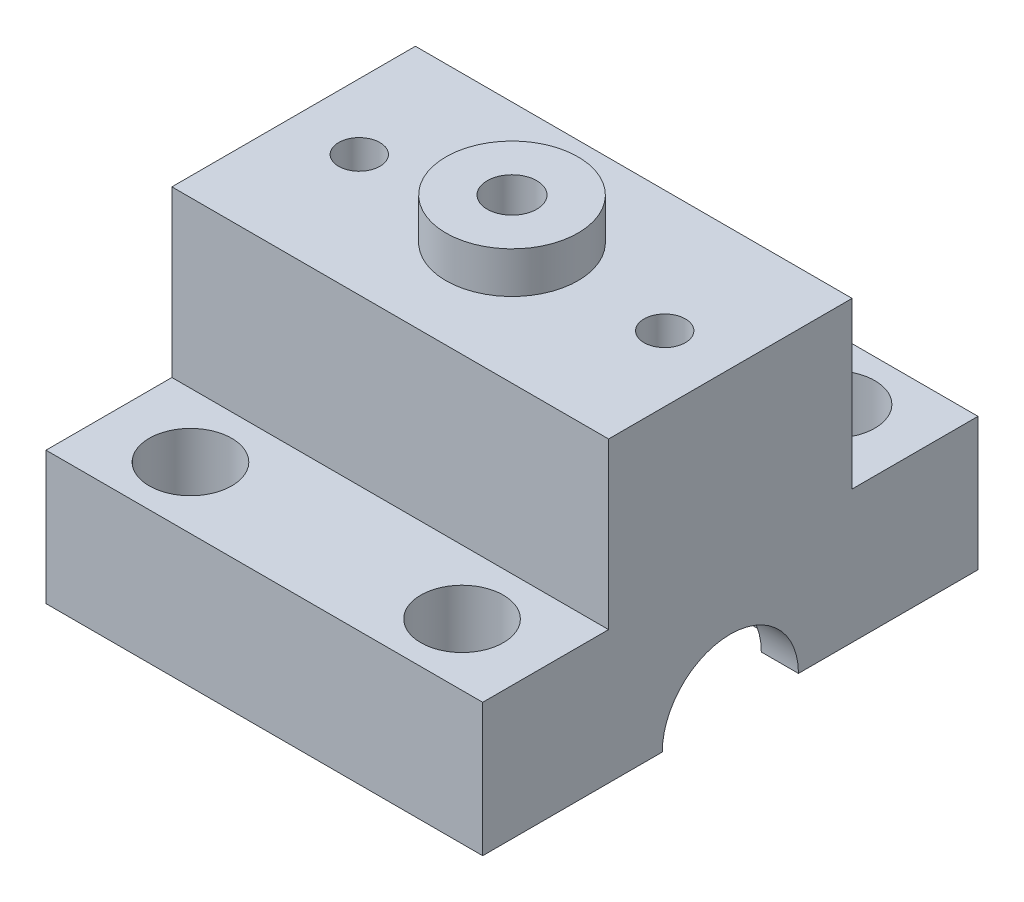
SolidWorks part; units mm, degrees
material "1060 Alloy"
ref_plane "Front Plane" through (0, 0, 0) normal (0, 0, 1) x (1, 0, 0)
ref_plane "Top Plane" through (0, 0, 0) normal (0, 1, 0) x (1, 0, 0)
ref_plane "Right Plane" through (0, 0, 0) normal (1, 0, 0) x (0, 0, -1)
sketch "Sketch1" plane through (0, 0, 0) normal (0, 1, 0) x (1, 0, 0)
  line L1 (-26.45, 15) -> (26.45, 15)
  line L2 (-26.45, 15) -> (-26.45, -15)
  line L3 (-26.45, -15) -> (26.45, -15)
  line L4 (26.45, 15) -> (26.45, -15)
  line L5 (-26.45, 15) -> (26.45, -15) construction
  line L6 (-26.45, -15) -> (26.45, 15) construction
  circle A0 centre (0, 0) radius 10.25
  point P0 (0, 0)
  dimension "D3" = 20.5
  dimension "D1" = 52.9
  dimension "D2" = 30
extrude "Boss-Extrude1" add sketch "Sketch1" along normal blind 5
sketch "Sketch2" plane through (0, 0, 0) normal (0, -1, 0) x (1, 0, 0)
  line L0 (-21.95, 10.5) -> (-21.95, -10.5)
  line L1 (-26.45, 15) -> (26.45, 15)
  line L2 (-26.45, 15) -> (-26.45, -15)
  line L3 (-26.45, -15) -> (26.45, -15)
  line L4 (26.45, 15) -> (26.45, -15)
  line L5 (-21.95, -10.5) -> (21.95, -10.5)
  line L6 (21.95, 10.5) -> (21.95, -10.5)
  line L7 (-21.95, 10.5) -> (21.95, 10.5)
  dimension "D1" = 4.5
extrude "Boss-Extrude2" add sketch "Sketch2" along normal blind 11.1
sketch "Sketch3" plane through (26.45, 0, 0) normal (1, 0, 0) x (0, 0, -1)
  line L0 (15, -11.1) -> (-15, -11.1) construction
  circle A0 centre (0, -11.1) radius 8.25
  dimension "D1" = 16.5
extrude "Cut-Extrude1" cut sketch "Sketch3" against normal through all
sketch "Sketch4" plane through (0, 0, -15) normal (0, 0, -1) x (-1, 0, 0)
  line L0 (26.45, 5) -> (26.45, -11.1) construction
  line L1 (-26.45, -11.1) -> (26.45, -11.1)
  line L2 (-26.45, -11.1) -> (-26.45, -6.1)
  line L3 (-26.45, -6.1) -> (26.45, -6.1)
  line L4 (26.45, -11.1) -> (26.45, -6.1)
  dimension "D1" = 5
extrude "Boss-Extrude3" add sketch "Sketch4" along normal blind 15
sketch "Sketch5" plane through (0, 0, 15) normal (0, 0, 1) x (1, 0, 0)
  line L0 (26.45, 5) -> (26.45, -11.1) construction
  line L1 (-26.45, -11.1) -> (26.45, -11.1)
  line L2 (-26.45, -11.1) -> (-26.45, -6.1)
  line L3 (-26.45, -6.1) -> (26.45, -6.1)
  line L4 (26.45, -11.1) -> (26.45, -6.1)
  dimension "D1" = 5
extrude "Boss-Extrude4" add sketch "Sketch5" along normal blind 15
sketch "Sketch7" plane through (0, 5, 0) normal (0, 1, 0) x (1, 0, 0)
  circle A0 centre (0, 0) radius 10.25
  circle A1 centre (0, 0) radius 14.75
  dimension "D1" = 4.5
extrude "Boss-Extrude5" add sketch "Sketch7" along normal blind 15
sketch "Sketch8" plane through (0, 20, 0) normal (0, 1, 0) x (1, 0, 0)
  circle A0 centre (0, 0) radius 14.75
  circle A1 centre (0, 0) radius 1.65
  dimension "D1" = 3.3
  dimension "D2" = 29.5
extrude "Boss-Extrude6" add sketch "Sketch8" along normal blind 5
sketch "Sketch9" plane through (0, 25, 0) normal (0, 1, 0) x (1, 0, 0)
  circle A0 centre (0, 0) radius 3
  circle A1 centre (0, 0) radius 8
  dimension "D1" = 6
  dimension "D2" = 5
extrude "Boss-Extrude7" add sketch "Sketch9" along normal blind 5
sketch "Sketch10" plane through (0, -6.1, 0) normal (0, 1, 0) x (1, 0, 0)
  line L1 (26.45, 30) -> (-26.45, 30)
  line L2 (26.45, 30) -> (26.45, 15)
  line L3 (26.45, 15) -> (-26.45, 15)
  line L4 (-26.45, 30) -> (-26.45, 15)
  line L5 (26.45, -15) -> (-26.45, -15)
  line L6 (26.45, -15) -> (26.45, -30)
  line L7 (26.45, -30) -> (-26.45, -30)
  line L8 (-26.45, -15) -> (-26.45, -30)
extrude "Boss-Extrude8" add sketch "Sketch10" along normal up to surface (11.1 mm away) up to face at (0, 5, 0)
sketch "Sketch11" plane through (0, -11.1, 0) normal (0, -1, 0) x (1, 0, 0)
  line L0 (-26.45, 30) -> (26.45, 30) construction
  line L1 (-26.45, 30) -> (-26.45, 8.25) construction
  line L2 (26.45, -30) -> (26.45, -8.25) construction
  line L3 (26.45, -30) -> (-26.45, -30) construction
  circle A0 centre (-16.45, 22.5) radius 2.5
  circle A1 centre (16.45, 22.5) radius 2.5
  circle A2 centre (16.45, -22.5) radius 2.5
  circle A3 centre (-16.45, -22.5) radius 2.5
  dimension "D1" = 7.5
  dimension "D2" = 10
  dimension "D3" = 10
  dimension "D4" = 7.5
  dimension "D5" = 5
  dimension "D6" = 5
  dimension "D7" = 5
  dimension "D8" = 5
sketch "Sketch12" plane through (0, 5, 0) normal (0, 1, 0) x (1, 0, 0)
  line L0 (26.45, 30) -> (-26.45, 30) construction
  line L1 (-26.45, 30) -> (-26.45, -30) construction
  line L2 (26.45, -30) -> (26.45, 30) construction
  line L3 (-26.45, -30) -> (26.45, -30) construction
  circle A0 centre (-16.45, -22.5) radius 5
  circle A1 centre (16.45, -22.5) radius 5
  circle A2 centre (16.45, 22.5) radius 5
  circle A3 centre (-16.45, 22.5) radius 5
  dimension "D1" = 10
  dimension "D2" = 10
  dimension "D3" = 10
  dimension "D4" = 10
  dimension "D6" = 10
  dimension "D7" = 10
  dimension "D8" = 7.5
  dimension "D5" = 7.5
extrude "Cut-Extrude2" cut sketch "Sketch12" against normal blind 8
sketch "Sketch13" plane through (0, -3, 0) normal (0, 1, 0) x (1, 0, 0)
  circle A0 centre (-16.45, -22.5) radius 2.2
  circle A1 centre (-16.45, 22.5) radius 2.2
  circle A2 centre (16.45, 22.5) radius 2.2
  circle A3 centre (16.45, -22.5) radius 2.2
  dimension "D1" = 4.4
  dimension "D2" = 4.4
  dimension "D3" = 4.4
  dimension "D4" = 4.4
extrude "Cut-Extrude3" cut sketch "Sketch13" against normal through all
sketch "Sketch14" plane through (0, 5, 0) normal (0, 1, 0) x (1, 0, 0)
  line L0 (-26.45, 30) -> (-26.45, -30) construction
  line L1 (-26.45, -14.75) -> (26.45, -14.75)
  line L2 (-26.45, -14.75) -> (-26.45, 14.75)
  line L3 (-26.45, 14.75) -> (26.45, 14.75)
  line L4 (26.45, -14.75) -> (26.45, 14.75)
  line L5 (26.45, -30) -> (26.45, 30) construction
  circle A0 centre (0, 0) radius 14.75
  line M6 (26.45, -30) -> (26.45, 30)
  line M8 (-26.45, 30) -> (-26.45, -30)
  circle M10 centre (0, 0) radius 14.75
  dimension "D3" = 29.5
  dimension "D1" = 29.5
  dimension "D2" = 14.75
extrude "Boss-Extrude11" add sketch "Sketch14" along normal up to surface (20 mm away) contours L3 L1 M8 M10 | L3 L1 M10 M6 up to face at (0, 25, 8)
sketch "Sketch16" plane through (0, 25, 0) normal (0, 1, 0) x (1, 0, 0)
  line L0 (-26.45, 14.75) -> (26.45, 14.75) construction
  line L1 (26.45, -14.75) -> (26.45, 14.75) construction
  line L2 (-26.45, 14.75) -> (-26.45, -14.75) construction
  circle A0 centre (18.5, 0) radius 2.5
  circle A2 centre (-18.5, 0) radius 2.5
  dimension "D1" = 5
  dimension "D2" = 14.75
  dimension "D3" = 7.95
  dimension "D4" = 5
  dimension "D5" = 7.95
  dimension "D6" = 14.75
extrude "Cut-Extrude4" cut sketch "Sketch16" against normal blind 5
sketch "Sketch17" plane through (0, 20, 0) normal (0, 1, 0) x (1, 0, 0)
  circle A0 centre (-18.5, 0) radius 1.5
  circle A1 centre (18.5, 0) radius 1.5
  dimension "D1" = 3
  dimension "D2" = 3
hole_wizard "M3 Tapped Hole1" positions "Sketch18" profile "Sketch19" tap size "M3" standard "ISO"
sketch "Sketch18" plane through (0, 20, 0) normal (0, 1, 0) x (1, 0, 0)
  point P0 (-18.5, 0)
  point P3 (18.5, 0)
sketch "Sketch19" plane through (-18.5, 20, 0) normal (1, 0, 0) x (0, 0, 1)
  line L0 (0, 0) -> (0, 11.5)
  line L1 (0, 11.5) -> (1.25, 10.7489)
  line L2 (1.25, 10.7489) -> (1.25, 0)
  line L5 (1.25, 0) -> (0, 0)
  line L10 (0, 11.5) -> (-1.25, 10.7489) construction
  line L11 (0, -6.35) -> (0, 107.95) construction
  dimension "Tap Drill Dia." = 2.5
  dimension "Tap Drill Depth" = 11.5
  dimension "Drill Angle" = 118
cosmetic thread "Hole Thread1" parameters "D1"=10, "D2"=3
cosmetic thread "Hole Thread2" parameters "D1"=10, "D2"=3
